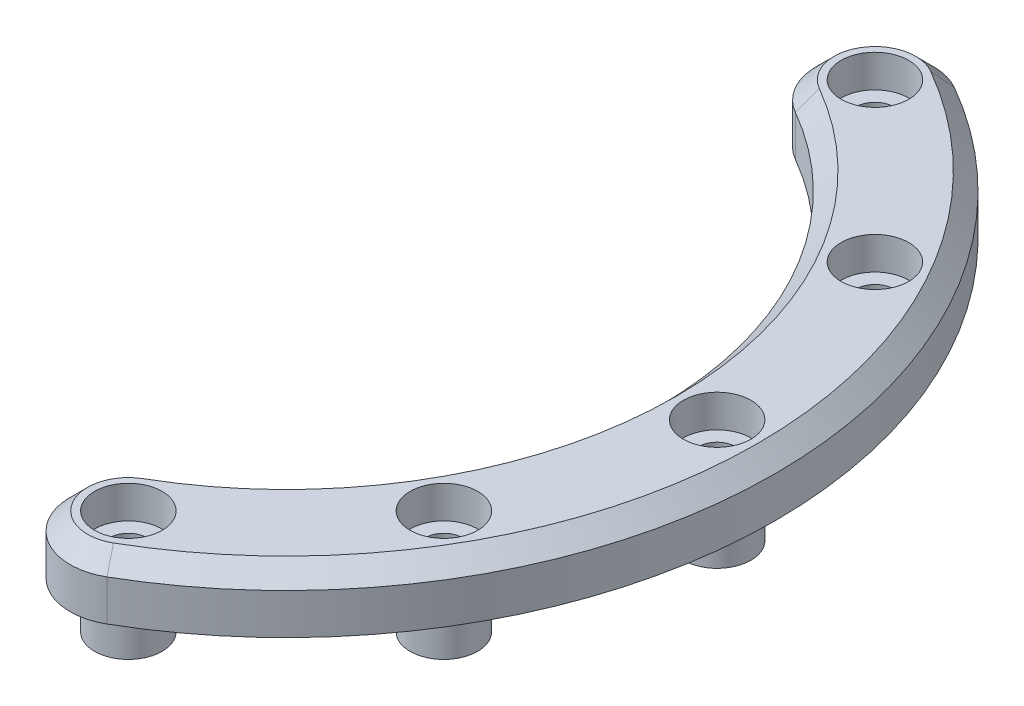
SolidWorks part; units mm, degrees
ref_plane "前视基准面" through (0, 0, 0) normal (0, 0, 1) x (1, 0, 0)
ref_plane "上视基准面" through (0, 0, 0) normal (0, 1, 0) x (1, 0, 0)
ref_plane "右视基准面" through (0, 0, 0) normal (1, 0, 0) x (0, 0, -1)
sketch "草图1" plane through (0, 0, 0) normal (0, 1, 0) x (1, 0, 0)
  arc A1 (21, -36.3731) -> (16, -27.7128) centre (18.5, -32.0429) cw
  arc A2 (21, 36.3731) -> (16, 27.7128) centre (18.5, 32.0429) ccw
  arc A3 (16, 27.7128) -> (16, -27.7128) centre (0, 0) cw
  arc A4 (21, 36.3731) -> (21, -36.3731) centre (0, 0) cw
extrude "凸台-拉伸1" add sketch "草图1" along normal blind 5
sketch "草图3" plane through (0, 0, 0) normal (0, -1, 0) x (1, 0, 0)
  circle A0 centre (18.5, 32.0429) radius 2.9
  circle A1 centre (32.0429, 18.5) radius 2.9
  circle A2 centre (37, 0) radius 2.9
  circle A3 centre (32.0429, -18.5) radius 2.9
  circle A4 centre (18.5, -32.0429) radius 2.9
  point P15 (0, 0)
  dimension "D1" = 5
extrude "凸台-拉伸3" add sketch "草图3" along normal blind 4
sketch "草图4" plane through (0, 5, 0) normal (0, 1, 0) x (1, 0, 0)
  circle A0 centre (18.5, 32.0429) radius 1.6
  circle A1 centre (32.0429, 18.5) radius 1.6
  circle A2 centre (37, 0) radius 1.6
  circle A3 centre (32.0429, -18.5) radius 1.6
  circle A4 centre (18.5, -32.0429) radius 1.6
  point P14 (0, 0)
  dimension "D1" = 5
extrude "切除-拉伸1" cut sketch "草图4" against normal through all
sketch "草图5" plane through (0, 5, 0) normal (0, 1, 0) x (1, 0, 0)
  circle A0 centre (18.5, 32.0429) radius 2.9
  circle A1 centre (32.0429, 18.5) radius 2.9
  circle A2 centre (37, 0) radius 2.9
  circle A3 centre (32.0429, -18.5) radius 2.9
  circle A4 centre (18.5, -32.0429) radius 2.9
  point P14 (0, 0)
  dimension "D1" = 5
extrude "切除-拉伸2" cut sketch "草图5" against normal blind 2.8
chamfer "倒角1" distance 1.5 angle 45 4 edges at (32, 5, 0) (14.1699, 5, 34.5429) (14.1699, 5, -34.5429) (42, 5, 0)
